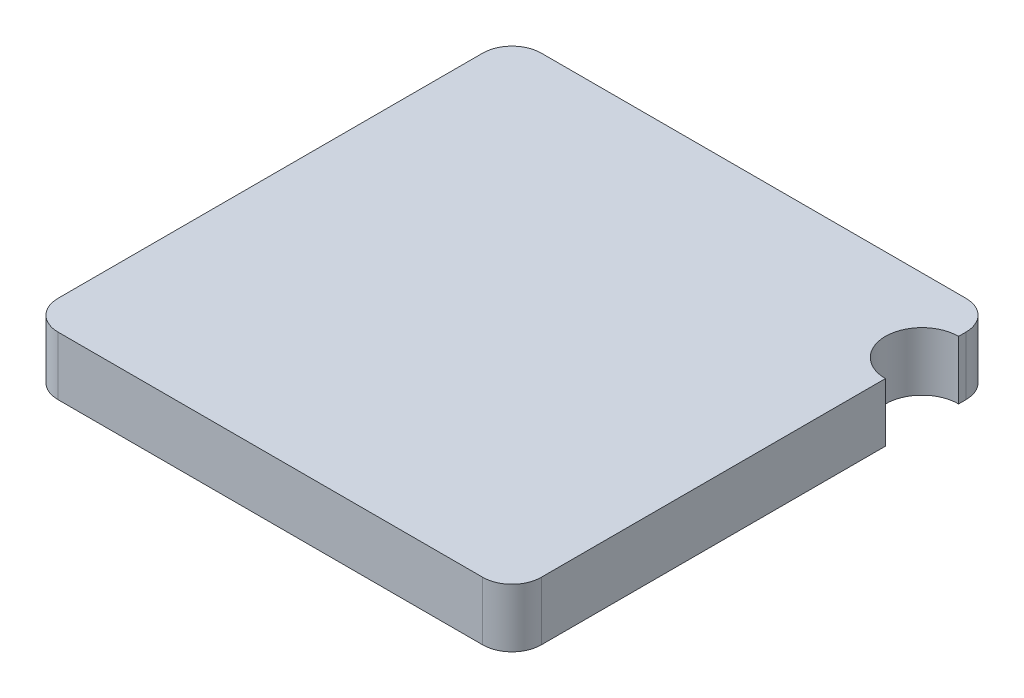
SolidWorks part; units mm, degrees
material "1060-H16"
ref_plane "Front Plane" through (0, 0, 0) normal (0, 0, 1) x (1, 0, 0)
ref_plane "Top Plane" through (0, 0, 0) normal (0, 1, 0) x (1, 0, 0)
ref_plane "Right Plane" through (0, 0, 0) normal (1, 0, 0) x (0, 0, -1)
sketch "Sketch1" plane through (0, 0, 0) normal (0, 1, 0) x (1, 0, 0)
  line L1 (-0.825, -0.825) -> (0.825, -0.825)
  line L2 (-0.825, -0.825) -> (-0.825, 0.825)
  line L3 (-0.825, 0.825) -> (0.825, 0.825)
  line L4 (0.825, -0.825) -> (0.825, 0.825)
  line L5 (-0.825, -0.825) -> (0.825, 0.825) construction
  line L6 (-0.825, 0.825) -> (0.825, -0.825) construction
  point P0 (0, 0)
  dimension "D1" = 1.65
extrude "Boss-Extrude1" add sketch "Sketch1" along normal blind 0.2
fillet "Fillet1" radius 0.1 4 edges at (0.825, 0.1, 0.825) (0.825, 0.1, -0.825) (-0.825, 0.1, -0.825) (-0.825, 0.1, 0.825)
sketch "Sketch2" plane through (0, 0.2, 0) normal (0, 1, 0) x (1, 0, 0)
  line L0 (0.825, -0.725) -> (0.825, 0.725) construction
  line L1 (0.725, 0.825) -> (-0.725, 0.825) construction
  circle A0 centre (0.825, 0.575) radius 0.125
  dimension "D1" = 0.25
  dimension "D2" = 0.25
extrude "Cut-Extrude1" cut sketch "Sketch2" against normal through all
